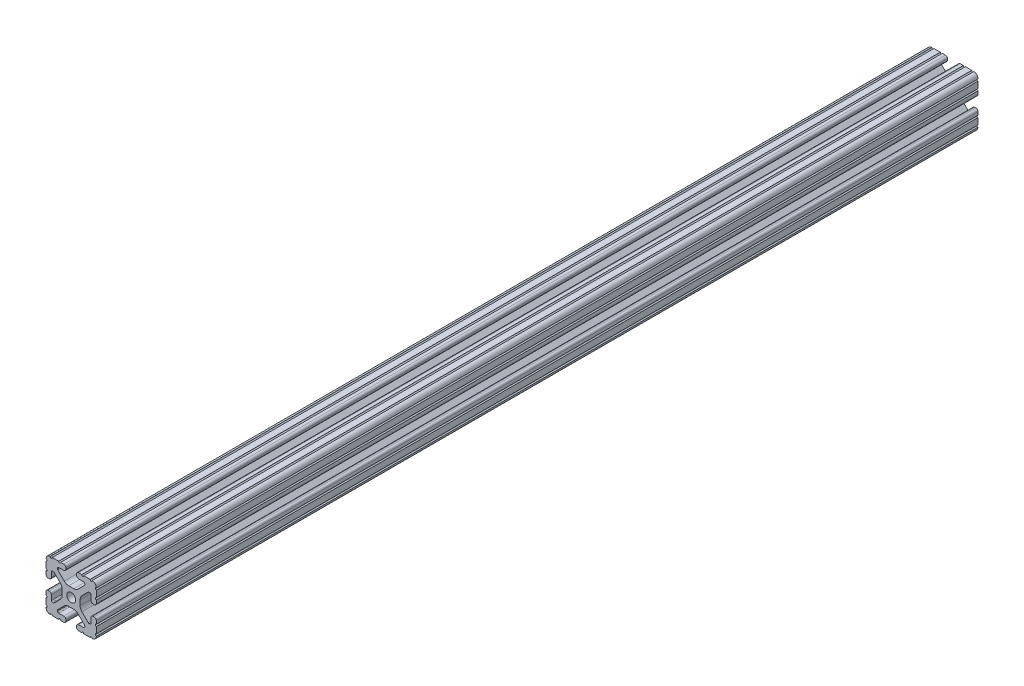
SolidWorks part; units mm, degrees
ref_plane "Front" through (0, 0, 0) normal (0, 0, 1) x (1, 0, 0)
ref_plane "Top" through (0, 0, 0) normal (0, 1, 0) x (1, 0, 0)
ref_plane "Right" through (0, 0, 0) normal (1, 0, 0) x (0, 0, -1)
sketch "Sketch1" plane through (0, 0, 0) normal (0, 0, 1) x (1, 0, 0)
  line L104 (-10.287, 13.5524) -> (-10.287, 14.0843)
  line L105 (-9.3853, 14.986) -> (-5.6176, 14.986)
  line L106 (-4.064, 16.5396) -> (-4.064, 17.4964)
  line L107 (-5.6176, 19.05) -> (-7.9742, 19.05)
  line L108 (-9.4982, 19.05) -> (-14.3277, 19.05)
  line L109 (-19.05, 14.3277) -> (-19.05, 9.4961)
  line L110 (-19.05, 7.9763) -> (-19.05, 5.6176)
  line L111 (-17.4964, 4.064) -> (-16.5396, 4.064)
  line L112 (-14.986, 5.6176) -> (-14.986, 9.3853)
  line L113 (-14.0843, 10.287) -> (-13.516, 10.287)
  line L114 (-12.8784, 10.0229) -> (-8.1476, 5.2921)
  line L115 (-6.7564, 1.9335) -> (-6.7564, -1.9335)
  line L116 (-8.1476, -5.2921) -> (-12.8784, -10.0229)
  line L117 (-13.516, -10.287) -> (-14.0843, -10.287)
  line L118 (-14.986, -9.3853) -> (-14.986, -5.6176)
  line L119 (-16.5396, -4.064) -> (-17.4964, -4.064)
  line L120 (-19.05, -5.6176) -> (-19.05, -7.9763)
  line L121 (-19.05, -9.4961) -> (-19.05, -14.3277)
  line L122 (-14.3277, -19.05) -> (-9.4961, -19.05)
  line L123 (-7.9763, -19.05) -> (-5.6176, -19.05)
  line L124 (-4.064, -17.4964) -> (-4.064, -16.5396)
  line L125 (-5.6176, -14.986) -> (-9.3853, -14.986)
  line L126 (-10.287, -14.0843) -> (-10.287, -13.5524)
  line L127 (-10.0229, -12.9148) -> (-5.2522, -8.144)
  line L128 (-1.9022, -6.7564) -> (1.9022, -6.7564)
  line L129 (5.2522, -8.144) -> (10.0229, -12.9148)
  line L130 (10.287, -13.5524) -> (10.287, -14.0843)
  line L131 (9.3853, -14.986) -> (5.6176, -14.986)
  line L132 (4.064, -16.5396) -> (4.064, -17.4964)
  line L133 (5.6176, -19.05) -> (7.9763, -19.05)
  line L134 (9.4961, -19.05) -> (14.3277, -19.05)
  line L135 (19.05, -14.3277) -> (19.05, -9.4961)
  line L136 (19.05, -7.9763) -> (19.05, -5.6176)
  line L137 (17.4964, -4.064) -> (16.5396, -4.064)
  line L138 (14.986, -5.6176) -> (14.986, -9.3853)
  line L139 (14.0843, -10.287) -> (13.516, -10.287)
  line L140 (12.8784, -10.0229) -> (8.1476, -5.2921)
  line L141 (6.7564, -1.9335) -> (6.7564, 1.9335)
  line L142 (8.1476, 5.2921) -> (12.8784, 10.0229)
  line L143 (13.516, 10.287) -> (14.0843, 10.287)
  line L144 (14.986, 9.3853) -> (14.986, 5.6176)
  line L145 (16.5396, 4.064) -> (17.4964, 4.064)
  line L146 (19.05, 5.6176) -> (19.05, 7.9763)
  line L147 (19.05, 9.4961) -> (19.05, 14.3277)
  line L148 (14.3277, 19.05) -> (9.4982, 19.05)
  line L149 (7.9742, 19.05) -> (5.6176, 19.05)
  line L150 (4.064, 17.4964) -> (4.064, 16.5396)
  line L151 (5.6176, 14.986) -> (9.3853, 14.986)
  line L152 (10.287, 14.0843) -> (10.287, 13.5524)
  line L153 (10.0229, 12.9148) -> (5.2522, 8.144)
  line L154 (1.9022, 6.7564) -> (-1.9022, 6.7564)
  line L155 (-5.2522, 8.144) -> (-10.0229, 12.9148)
  circle A1 centre (0, 0) radius 3.3274
  arc A120 (-9.3853, 14.986) -> (-10.287, 14.0843) centre (-9.3853, 14.0843) ccw
  arc A121 (-5.6176, 14.986) -> (-4.064, 16.5396) centre (-5.6176, 16.5396) ccw
  arc A122 (-4.064, 17.4964) -> (-5.6176, 19.05) centre (-5.6176, 17.4964) ccw
  arc A123 (-9.4982, 19.05) -> (-7.9742, 19.05) centre (-8.7362, 19.05) ccw
  arc A124 (-15.8475, 19.05) -> (-14.3277, 19.05) centre (-15.0876, 18.9933) ccw
  arc A125 (-15.8475, 19.05) -> (-19.05, 15.8475) centre (-15.8751, 15.8751) ccw
  arc A126 (-19.05, 14.3277) -> (-19.05, 15.8475) centre (-18.9933, 15.0876) ccw
  arc A127 (-19.05, 7.9763) -> (-19.05, 9.4961) centre (-18.9933, 8.7362) ccw
  arc A128 (-19.05, 5.6176) -> (-17.4964, 4.064) centre (-17.4964, 5.6176) ccw
  arc A129 (-16.5396, 4.064) -> (-14.986, 5.6176) centre (-16.5396, 5.6176) ccw
  arc A130 (-14.0843, 10.287) -> (-14.986, 9.3853) centre (-14.0843, 9.3853) ccw
  arc A131 (-12.8784, 10.0229) -> (-13.516, 10.287) centre (-13.516, 9.3853) ccw
  arc A132 (-6.7564, 1.9335) -> (-8.1476, 5.2921) centre (-11.5062, 1.9335) ccw
  arc A133 (-8.1476, -5.2921) -> (-6.7564, -1.9335) centre (-11.5062, -1.9335) ccw
  arc A134 (-13.516, -10.287) -> (-12.8784, -10.0229) centre (-13.516, -9.3853) ccw
  arc A135 (-14.986, -9.3853) -> (-14.0843, -10.287) centre (-14.0843, -9.3853) ccw
  arc A136 (-14.986, -5.6176) -> (-16.5396, -4.064) centre (-16.5396, -5.6176) ccw
  arc A137 (-17.4964, -4.064) -> (-19.05, -5.6176) centre (-17.4964, -5.6176) ccw
  arc A138 (-19.05, -9.4961) -> (-19.05, -7.9763) centre (-18.9933, -8.7362) ccw
  arc A139 (-19.05, -15.8475) -> (-19.05, -14.3277) centre (-18.9933, -15.0876) ccw
  arc A140 (-19.05, -15.8475) -> (-15.8475, -19.05) centre (-15.8751, -15.8751) ccw
  arc A141 (-14.3277, -19.05) -> (-15.8475, -19.05) centre (-15.0876, -18.9933) ccw
  arc A142 (-7.9763, -19.05) -> (-9.4961, -19.05) centre (-8.7362, -18.9933) ccw
  arc A143 (-5.6176, -19.05) -> (-4.064, -17.4964) centre (-5.6176, -17.4964) ccw
  arc A144 (-4.064, -16.5396) -> (-5.6176, -14.986) centre (-5.6176, -16.5396) ccw
  arc A145 (-10.287, -14.0843) -> (-9.3853, -14.986) centre (-9.3853, -14.0843) ccw
  arc A146 (-10.0229, -12.9148) -> (-10.287, -13.5524) centre (-9.3853, -13.5524) ccw
  arc A147 (-1.9022, -6.7564) -> (-5.2522, -8.144) centre (-1.9022, -11.494) ccw
  arc A148 (5.2522, -8.144) -> (1.9022, -6.7564) centre (1.9022, -11.494) ccw
  arc A149 (10.287, -13.5524) -> (10.0229, -12.9148) centre (9.3853, -13.5524) ccw
  arc A150 (9.3853, -14.986) -> (10.287, -14.0843) centre (9.3853, -14.0843) ccw
  arc A151 (5.6176, -14.986) -> (4.064, -16.5396) centre (5.6176, -16.5396) ccw
  arc A152 (4.064, -17.4964) -> (5.6176, -19.05) centre (5.6176, -17.4964) ccw
  arc A153 (9.4961, -19.05) -> (7.9763, -19.05) centre (8.7362, -18.9933) ccw
  arc A154 (15.8475, -19.05) -> (14.3277, -19.05) centre (15.0876, -18.9933) ccw
  arc A155 (15.8475, -19.05) -> (19.05, -15.8475) centre (15.8751, -15.8751) ccw
  arc A156 (19.05, -14.3277) -> (19.05, -15.8475) centre (18.9933, -15.0876) ccw
  arc A157 (19.05, -7.9763) -> (19.05, -9.4961) centre (18.9933, -8.7362) ccw
  arc A158 (19.05, -5.6176) -> (17.4964, -4.064) centre (17.4964, -5.6176) ccw
  arc A159 (16.5396, -4.064) -> (14.986, -5.6176) centre (16.5396, -5.6176) ccw
  arc A160 (14.0843, -10.287) -> (14.986, -9.3853) centre (14.0843, -9.3853) ccw
  arc A161 (12.8784, -10.0229) -> (13.516, -10.287) centre (13.516, -9.3853) ccw
  arc A162 (6.7564, -1.9335) -> (8.1476, -5.2921) centre (11.5062, -1.9335) ccw
  arc A163 (8.1476, 5.2921) -> (6.7564, 1.9335) centre (11.5062, 1.9335) ccw
  arc A164 (13.516, 10.287) -> (12.8784, 10.0229) centre (13.516, 9.3853) ccw
  arc A165 (14.986, 9.3853) -> (14.0843, 10.287) centre (14.0843, 9.3853) ccw
  arc A166 (14.986, 5.6176) -> (16.5396, 4.064) centre (16.5396, 5.6176) ccw
  arc A167 (17.4964, 4.064) -> (19.05, 5.6176) centre (17.4964, 5.6176) ccw
  arc A168 (19.05, 9.4961) -> (19.05, 7.9763) centre (18.9933, 8.7362) ccw
  arc A169 (19.05, 15.8475) -> (19.05, 14.3277) centre (18.9933, 15.0876) ccw
  arc A170 (19.05, 15.8475) -> (15.8475, 19.05) centre (15.8751, 15.8751) ccw
  arc A171 (14.3277, 19.05) -> (15.8475, 19.05) centre (15.0876, 18.9933) ccw
  arc A172 (7.9742, 19.05) -> (9.4982, 19.05) centre (8.7362, 19.05) ccw
  arc A173 (5.6176, 19.05) -> (4.064, 17.4964) centre (5.6176, 17.4964) ccw
  arc A174 (4.064, 16.5396) -> (5.6176, 14.986) centre (5.6176, 16.5396) ccw
  arc A175 (10.287, 14.0843) -> (9.3853, 14.986) centre (9.3853, 14.0843) ccw
  arc A176 (10.0229, 12.9148) -> (10.287, 13.5524) centre (9.3853, 13.5524) ccw
  arc A177 (1.9022, 6.7564) -> (5.2522, 8.144) centre (1.9022, 11.494) ccw
  arc A178 (-5.2522, 8.144) -> (-1.9022, 6.7564) centre (-1.9022, 11.494) ccw
  arc A179 (-10.287, 13.5524) -> (-10.0229, 12.9148) centre (-9.3853, 13.5524) ccw
extrude "Boss-Extrude1" add sketch "Sketch1" along normal mid plane 1219.2
sketch "Sketch2" plane through (19.05, 0, 0) normal (1, 0, 0) x (0, 0, -1)
  line L0 (57.5873, -19.0498) -> (57.5873, 31.6772) construction
  line L1 (57.5873, 24.697) -> (57.5873, -26.6574)
  line L2 (57.5873, -26.6574) -> (613.3248, -26.6574)
  line L3 (613.3248, -26.6574) -> (613.3248, 24.697)
  line L4 (613.3248, 24.697) -> (57.5873, 24.697)
extrude "Cut-Extrude1" cut sketch "Sketch2" against normal blind 41.148 and the other way blind 5.08
